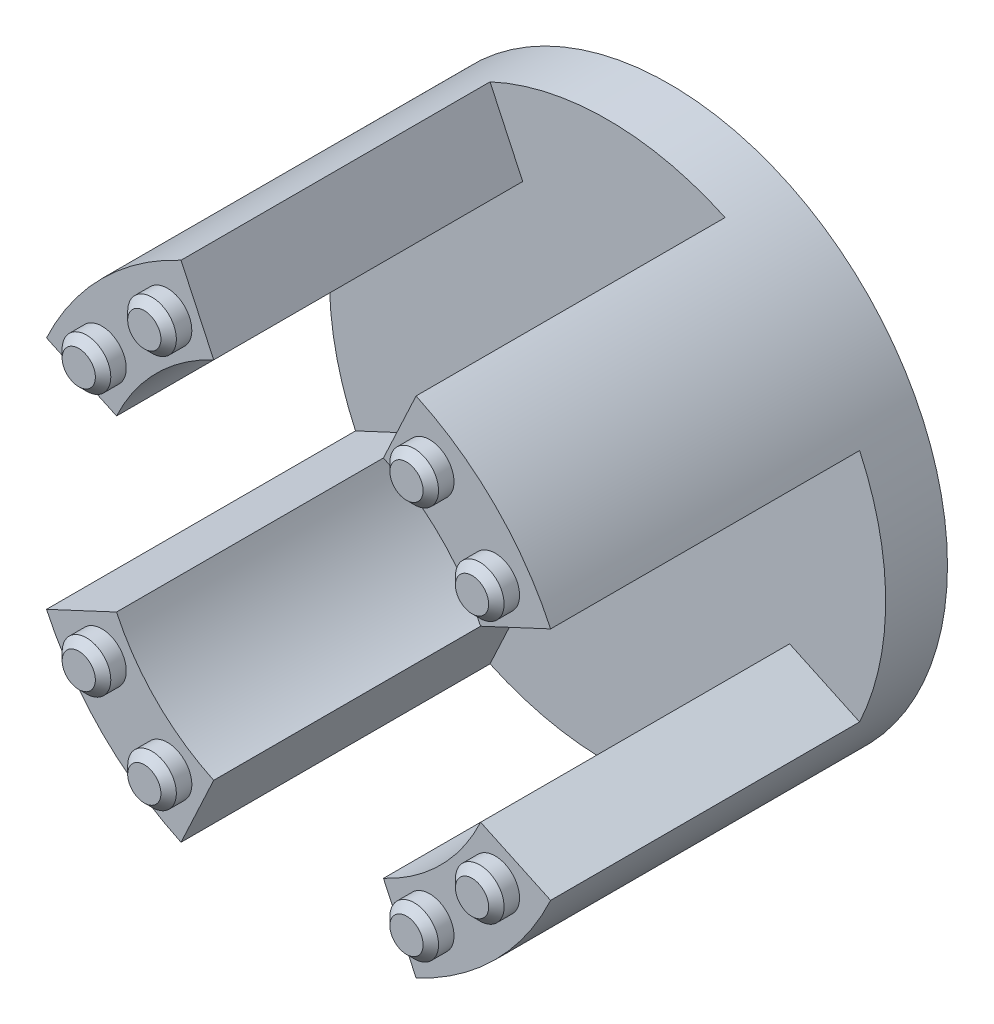
SolidWorks part; units mm, degrees
ref_plane "正面" through (0, 0, 0) normal (0, 0, 1) x (1, 0, 0)
ref_plane "平面" through (0, 0, 0) normal (0, 1, 0) x (1, 0, 0)
ref_plane "右側面" through (0, 0, 0) normal (1, 0, 0) x (0, 0, -1)
sketch "ｽｹｯﾁ1" plane through (0, 0, 0) normal (0, 0, 1) x (1, 0, 0)
  circle A0 centre (0, 0) radius 18
  circle A2 centre (0, 3) radius 1
  circle A3 centre (3, 0) radius 1
  circle A4 centre (0, -3) radius 1
  circle A5 centre (-3, 0) radius 1
  point P15 (0, 0)
  dimension "D1" = 36
  dimension "D3" = 2
  dimension "D4" = 3
  dimension "D5" = 4
extrude "ﾎﾞｽ - 押し出し1" add sketch "ｽｹｯﾁ1" along normal blind 4
sketch "ｽｹｯﾁ2" plane through (0, 0, 4) normal (0, 0, 1) x (1, 0, 0)
  line L0 (0, 0) -> (0, -18) construction
  line L1 (18, 0) -> (0, 0) construction
  line L2 (16.3135, -7.6071) -> (11.782, -5.494)
  line L3 (5.494, -11.782) -> (7.6071, -16.3135)
  line L4 (0, 0) -> (11.782, -5.494) construction
  line L5 (0, 0) -> (5.494, -11.782) construction
  arc A0 (5.494, -11.782) -> (11.782, -5.494) centre (0, 0) ccw
  circle A1 centre (0, 0) radius 18
  arc A2 (7.6071, -16.3135) -> (16.3135, -7.6071) centre (0, 0) ccw
  circle A4 centre (0, 0) radius 18 construction
  circle A5 centre (0, 0) radius 13 construction
  point P4 (13, 0)
  point P8 (17.2135, 5.2627)
  dimension "D3" = 25
  dimension "D4" = 25
  dimension "D1" = 0
  dimension "D2" = 5
extrude "ﾎﾞｽ - 押し出し2" add sketch "ｽｹｯﾁ2" along normal blind 20
ref_axis "軸1" through (0, 0, 24) along (0, 0, -1)
pattern_circular "円形ﾊﾟﾀｰﾝ1" count 4 over 360 about axis through (0, 0, 24) along (0, 0, -1) of "ﾎﾞｽ - 押し出し2"
sketch "ｽｹｯﾁ3" plane through (0, 0, 24) normal (0, 0, 1) x (1, 0, 0)
  line L0 (0, 0) -> (12.7279, 12.7279) construction
  line L1 (8.4853, 12.7279) -> (12.7279, 8.4853) construction
  arc A0 (16.3135, 7.6071) -> (7.6071, 16.3135) centre (0, 0) ccw construction
  circle A1 centre (8.4853, 12.7279) radius 1.575
  circle A2 centre (12.7279, 8.4853) radius 1.575
  point P8 (10.6066, 10.6066)
  dimension "D1" = 3.15
  dimension "D2" = 15
  dimension "D3" = 3
extrude "ﾎﾞｽ - 押し出し3" add sketch "ｽｹｯﾁ3" along normal blind 1.5
pattern_circular "円形ﾊﾟﾀｰﾝ2" count 4 over 360 about axis through (0, 0, 0) along (0, 0, 1) of "ﾎﾞｽ - 押し出し3"
sketch "ｽｹｯﾁ4" plane through (0, 0, 0) normal (0, 0, -1) x (-1, 0, 0)
  circle A0 centre (0, 0) radius 6.25
  dimension "D1" = 12.5
extrude "ｶｯﾄ - 押し出し1" cut sketch "ｽｹｯﾁ4" against normal blind 2
chamfer "面取り1" distance 0.5 angle 45 8 edges at (-10.0603, -12.7279, 25.5) (-14.3029, -8.4853, 25.5) (-12.7279, 10.0603, 25.5) (-8.4853, 14.3029, 25.5) (10.0603, 12.7279, 25.5) (14.3029, 8.4853, 25.5) (12.7279, -10.0603, 25.5) (8.4853, -14.3029, 25.5)
